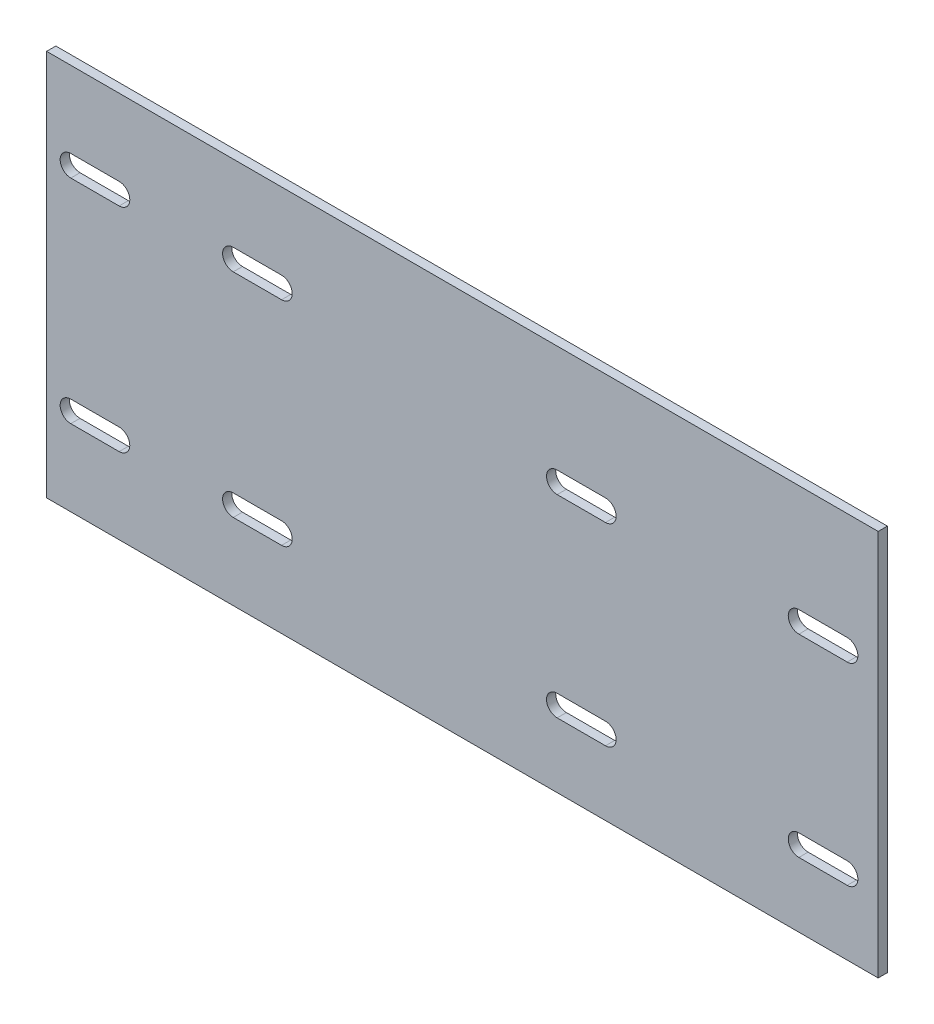
SolidWorks part; units mm, degrees
material "AISI 1020"
ref_plane "Frontal" through (0, 0, 0) normal (0, 0, 1) x (1, 0, 0)
ref_plane "Superior" through (0, 0, 0) normal (0, 1, 0) x (1, 0, 0)
ref_plane "Direito" through (0, 0, 0) normal (1, 0, 0) x (0, 0, -1)
sketch "Esboço1" plane through (0, 0, 0) normal (0, 0, 1) x (1, 0, 0)
  line L1 (-215, -100) -> (215, -100)
  line L2 (-215, -100) -> (-215, 100)
  line L3 (-215, 100) -> (215, 100)
  line L4 (215, -100) -> (215, 100)
  line L5 (-215, -100) -> (215, 100) construction
  line L6 (-215, 100) -> (215, -100) construction
  point P0 (0, 0)
  dimension "D1" = 430
  dimension "D2" = 200
extrude "Ressalto-extrusão1" add sketch "Esboço1" along normal blind 4.7625
sketch "Esboço2" plane through (0, 0, 4.7625) normal (0, 0, 1) x (1, 0, 0)
  line L0 (-215, 100) -> (-215, -100) construction
  line L1 (-106, -55) -> (-190, -55) construction
  line L2 (-106, -55) -> (-106, 55) construction
  line L3 (-106, 55) -> (-190, 55) construction
  line L4 (-190, -55) -> (-190, 55) construction
  line L5 (-106, -55) -> (-190, 55) construction
  line L6 (-106, 55) -> (-190, -55) construction
  line L7 (61.5, -61) -> (186.5, -61) construction
  line L8 (61.5, -61) -> (61.5, 39) construction
  line L9 (61.5, 39) -> (186.5, 39) construction
  line L10 (186.5, -61) -> (186.5, 39) construction
  line L11 (61.5, -61) -> (186.5, 39) construction
  line L12 (61.5, 39) -> (186.5, -61) construction
  line L13 (-202.5, 55) -> (-177.5, 55) construction
  line L14 (-202.5, 60.5) -> (-177.5, 60.5)
  line L15 (-202.5, 49.5) -> (-177.5, 49.5)
  line L16 (-93.5, 55) -> (-118.5, 55) construction
  line L17 (-93.5, 49.5) -> (-118.5, 49.5)
  line L18 (-93.5, 60.5) -> (-118.5, 60.5)
  line L19 (-202.5, -55) -> (-177.5, -55) construction
  line L20 (-202.5, -49.5) -> (-177.5, -49.5)
  line L21 (-202.5, -60.5) -> (-177.5, -60.5)
  line L22 (-93.5, -55) -> (-118.5, -55) construction
  line L23 (-93.5, -60.5) -> (-118.5, -60.5)
  line L24 (-93.5, -49.5) -> (-118.5, -49.5)
  line L25 (49, 39) -> (74, 39) construction
  line L26 (49, 44.5) -> (74, 44.5)
  line L27 (49, 33.5) -> (74, 33.5)
  line L28 (199, 39) -> (174, 39) construction
  line L29 (199, 33.5) -> (174, 33.5)
  line L30 (199, 44.5) -> (174, 44.5)
  line L31 (49, -61) -> (74, -61) construction
  line L32 (49, -55.5) -> (74, -55.5)
  line L33 (49, -66.5) -> (74, -66.5)
  line L34 (199, -61) -> (174, -61) construction
  line L35 (199, -66.5) -> (174, -66.5)
  line L36 (199, -55.5) -> (174, -55.5)
  arc A0 (-202.5, 60.5) -> (-202.5, 49.5) centre (-202.5, 55) ccw
  arc A1 (-177.5, 49.5) -> (-177.5, 60.5) centre (-177.5, 55) ccw
  arc A2 (-93.5, 49.5) -> (-93.5, 60.5) centre (-93.5, 55) ccw
  arc A3 (-118.5, 60.5) -> (-118.5, 49.5) centre (-118.5, 55) ccw
  arc A4 (-202.5, -49.5) -> (-202.5, -60.5) centre (-202.5, -55) ccw
  arc A5 (-177.5, -60.5) -> (-177.5, -49.5) centre (-177.5, -55) ccw
  arc A6 (-93.5, -60.5) -> (-93.5, -49.5) centre (-93.5, -55) ccw
  arc A7 (-118.5, -49.5) -> (-118.5, -60.5) centre (-118.5, -55) ccw
  arc A8 (49, 44.5) -> (49, 33.5) centre (49, 39) ccw
  arc A9 (74, 33.5) -> (74, 44.5) centre (74, 39) ccw
  arc A10 (199, 33.5) -> (199, 44.5) centre (199, 39) ccw
  arc A11 (174, 44.5) -> (174, 33.5) centre (174, 39) ccw
  arc A12 (49, -55.5) -> (49, -66.5) centre (49, -61) ccw
  arc A13 (74, -66.5) -> (74, -55.5) centre (74, -61) ccw
  arc A14 (199, -66.5) -> (199, -55.5) centre (199, -61) ccw
  arc A15 (174, -55.5) -> (174, -66.5) centre (174, -61) ccw
  point P0 (-148, 0)
  point P5 (124, -11)
  point P15 (-190, 55)
  point P21 (-106, 55)
  point P28 (-190, -55)
  point P35 (-106, -55)
  point P43 (61.5, 39)
  point P49 (186.5, 39)
  point P57 (61.5, -61)
  point P63 (186.5, -61)
  dimension "D8" = 5.5
  dimension "D9" = 5.5
  dimension "D1" = 84
  dimension "D2" = 110
  dimension "D3" = 25
  dimension "D4" = 125
  dimension "D5" = 100
  dimension "D6" = 11
  dimension "D7" = 25
  dimension "D10" = 272
extrude "Corte-extrusão1" cut sketch "Esboço2" against normal through all
ref_plane "Plano1" through (0, -55, 0) normal (0, 1, 0) x (-1, 0, 0)
